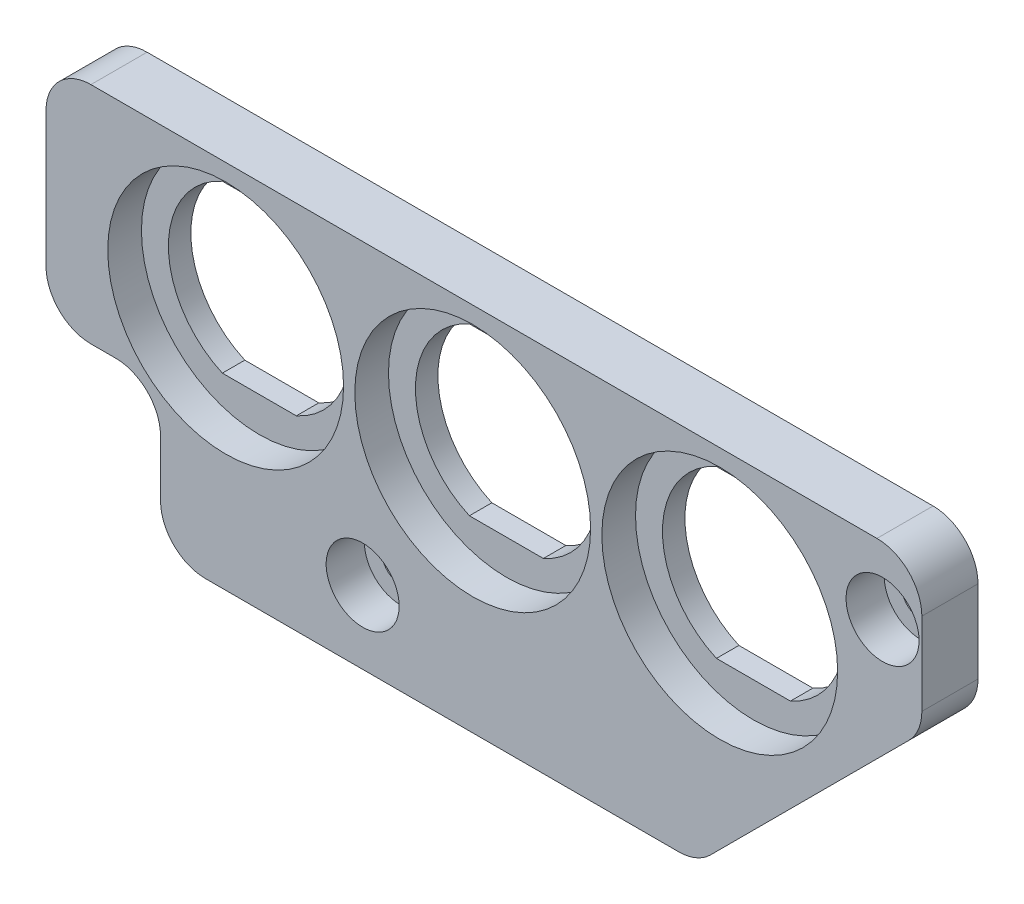
SolidWorks part; units mm, degrees
material "Alumine"
ref_plane "Plan de face" through (0, 0, 0) normal (0, 0, 1) x (1, 0, 0)
ref_plane "Plan de dessus" through (0, 0, 0) normal (0, 1, 0) x (1, 0, 0)
ref_plane "Plan de droite" through (0, 0, 0) normal (1, 0, 0) x (0, 0, -1)
sketch "Esquisse1" plane through (0, 0, 0) normal (0, 0, 1) x (1, 0, 0)
  line L0 (-29.9768, -25.0776) -> (17.8232, -25.0776)
  line L1 (-29.9768, -25.0776) -> (-29.9768, -12.0776)
  line L2 (-30.1768, 7.9224) -> (37.8232, 7.9224)
  line L3 (37.8232, -5.0776) -> (37.8232, 7.9224)
  line L4 (17.8232, -25.0776) -> (37.8232, -5.0776)
  line L6 (-30.1768, 7.9224) -> (-40.1768, 7.9224)
  line L8 (-29.9768, -12.0776) -> (-40.1768, -12.0776)
  line L9 (-40.1768, 7.9224) -> (-40.1768, -12.0776)
  point P3 (37.8232, -25.0776)
  dimension "D1" = 33
  dimension "D2" = 13
  dimension "D3" = 10
  dimension "D4" = 68
  dimension "D5" = 67.8
extrude "Boss.-Extru.1" add sketch "Esquisse1" along normal blind 5
fillet "Congé1" radius 4 7 edges at (-29.9768, -25.0776, 2.5) (37.8232, 7.9224, 2.5) (17.8232, -25.0776, 2.5) (37.8232, -5.0776, 2.5) (-40.1768, 7.9224, 2.5) (-29.9768, -12.0776, 2.5) (-40.1768, -12.0776, 2.5)
sketch "Esquisse2" plane through (0, 0, 5) normal (0, 0, 1) x (1, 0, 0)
  line L0 (-5.4707, 3.3224) -> (1.1172, 3.3224)
  line L1 (16.5293, 3.3224) -> (23.1172, 3.3224)
  line L2 (23.1172, -11.4776) -> (16.5293, -11.4776)
  line L3 (1.1172, -11.4776) -> (-5.4707, -11.4776)
  line L4 (-27.4707, 3.3224) -> (-20.8828, 3.3224)
  line L5 (-20.8828, -11.4776) -> (-27.4707, -11.4776)
  line L6 (-25.9768, -25.0776) -> (16.1664, -25.0776) construction
  line L8 (37.8232, -3.4208) -> (37.8232, 3.9224) construction
  arc A0 (1.1172, -11.4776) -> (1.1172, 3.3224) centre (-2.1768, -4.0776) ccw
  arc A1 (16.5293, 3.3224) -> (16.5293, -11.4776) centre (19.8232, -4.0776) ccw
  arc A2 (-5.4707, 3.3224) -> (-5.4707, -11.4776) centre (-2.1768, -4.0776) ccw
  arc A3 (23.1172, -11.4776) -> (23.1172, 3.3224) centre (19.8232, -4.0776) ccw
  arc A6 (-20.8828, -11.4776) -> (-20.8828, 3.3224) centre (-24.1768, -4.0776) ccw
  arc A7 (-27.4707, 3.3224) -> (-27.4707, -11.4776) centre (-24.1768, -4.0776) ccw
  dimension "D1" = 16.2
  dimension "D5" = 8.1
  dimension "D4" = 8.1
  dimension "D2" = 7.4
  dimension "D3" = 7.4
  dimension "D6" = 22
  dimension "D7" = 22
  dimension "D8" = 21
  dimension "D9" = 18
extrude "Enlèv. mat.-Extru.1" cut sketch "Esquisse2" against normal blind 10
sketch "Esquisse5" plane through (0, 0, 5) normal (0, 0, 1) x (1, 0, 0)
  circle A0 centre (19.8232, -4.0776) radius 10.5
  circle A1 centre (-2.1768, -4.0776) radius 10.5
  circle A2 centre (-24.1768, -4.0776) radius 10.5
  dimension "D1" = 21
extrude "Enlèv. mat.-Extru.3" cut sketch "Esquisse5" against normal blind 3
hole_wizard "Chambrage pour vis à tête hexagonale M31" positions "Esquisse6" profile "Esquisse7" counterbore size "M3" standard "ISO" end condition through all
sketch "Esquisse6" plane through (0, 0, 5) normal (0, 0, 1) x (1, 0, 0)
  line L0 (37.8232, -3.4208) -> (37.8232, 3.9224) construction
  line L2 (33.8232, 7.9224) -> (-36.1768, 7.9224) construction
  line L3 (-29.9768, -16.0776) -> (-29.9768, -21.0776) construction
  line L4 (-25.9768, -25.0776) -> (16.1664, -25.0776) construction
  point P0 (34.3232, 1.9224)
  point P4 (-11.9768, -18.5776)
  dimension "D1" = 3.5
  dimension "D2" = 6.5
  dimension "D3" = 6
  dimension "D5" = 18
sketch "Esquisse7" plane through (34.3232, 1.9224, 5) normal (1, 0, 0) x (0, -1, 0)
  line L0 (0, 0) -> (0, 5)
  line L1 (0, 5) -> (1.7, 5)
  line L3 (1.7, 5) -> (1.7, 3.4)
  line L4 (1.7, 3.4) -> (3.25, 3.4)
  line L5 (3.25, 3.4) -> (3.25, 0)
  line L7 (3.25, 0) -> (0, 0)
  line L11 (0, -6.35) -> (0, 107.95) construction
  dimension "Diamètre du perçage jusqu'au prochain" = 3.4
  dimension "Profondeur du perçage jusqu'au prochain" = 5
  dimension "Diamètre du chambrage" = 6.5
  dimension "Profondeur du chambrage" = 3.4
